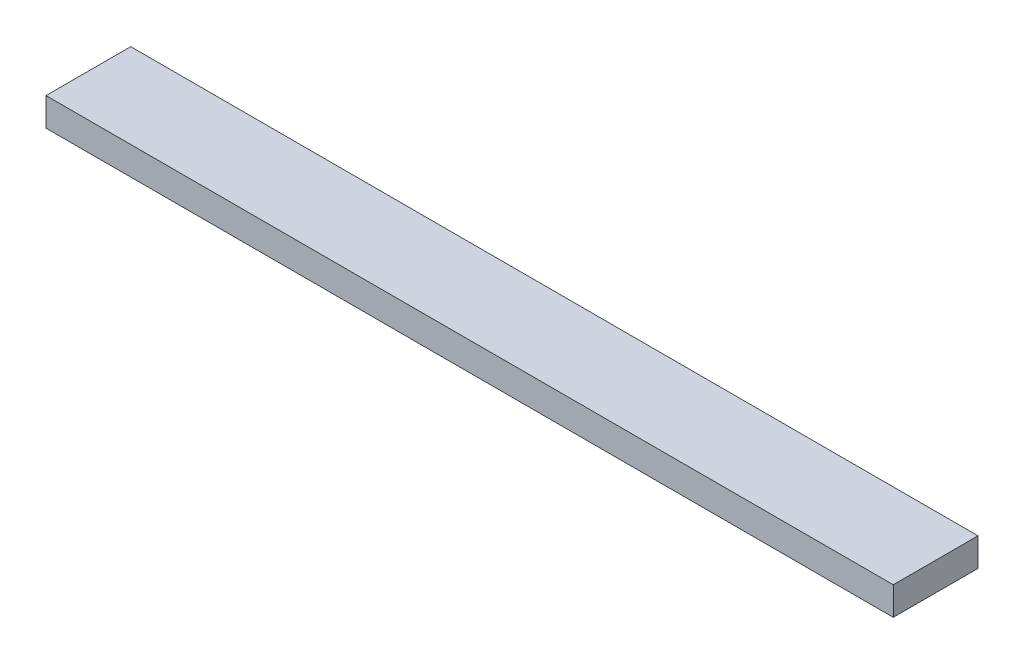
SolidWorks part; units mm, degrees
material "6061 Alloy"
ref_plane "Front Plane" through (0, 0, 0) normal (0, 0, 1) x (1, 0, 0)
ref_plane "Top Plane" through (0, 0, 0) normal (0, 1, 0) x (1, 0, 0)
ref_plane "Right Plane" through (0, 0, 0) normal (1, 0, 0) x (0, 0, -1)
sketch "Sketch1" plane through (0, 0, 0) normal (0, 1, 0) x (1, 0, 0)
  line L1 (-150, -15) -> (150, -15)
  line L2 (-150, -15) -> (-150, 15)
  line L3 (-150, 15) -> (150, 15)
  line L4 (150, -15) -> (150, 15)
  line L5 (-150, -15) -> (150, 15) construction
  line L6 (-150, 15) -> (150, -15) construction
  point P0 (0, 0)
  dimension "D1" = 300
  dimension "D2" = 30
extrude "Boss-Extrude1" add sketch "Sketch1" along normal blind 10
